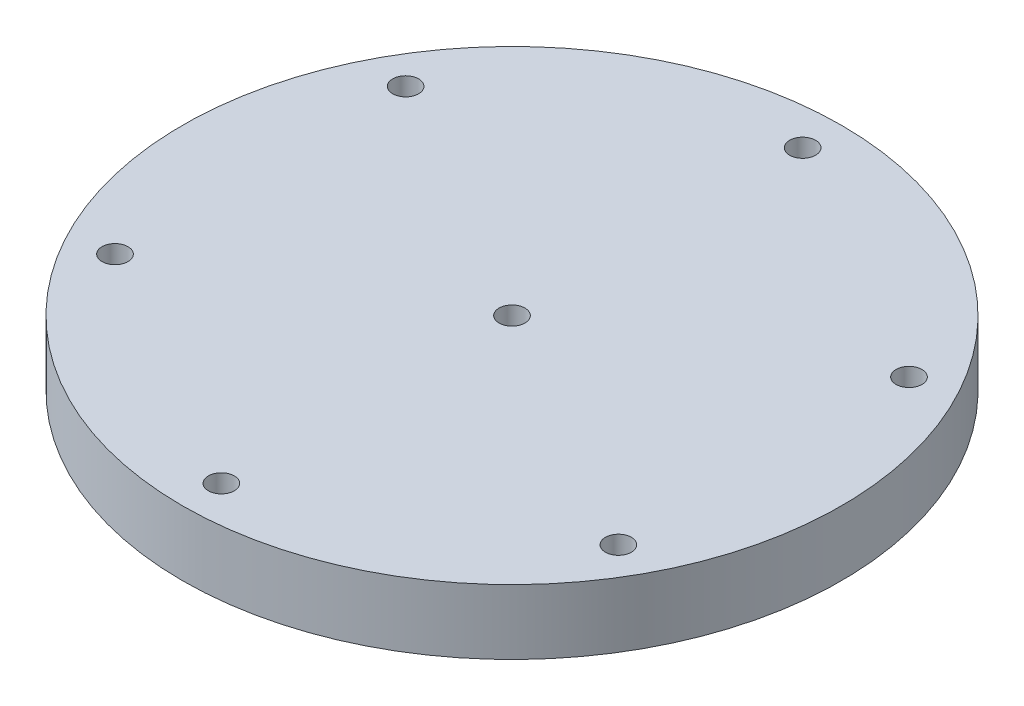
SolidWorks part; units mm, degrees
ref_plane "Front Plane" through (0, 0, 0) normal (0, 0, 1) x (1, 0, 0)
ref_plane "Top Plane" through (0, 0, 0) normal (0, 1, 0) x (1, 0, 0)
ref_plane "Right Plane" through (0, 0, 0) normal (1, 0, 0) x (0, 0, -1)
sketch "Sketch1" plane through (0, 0, 0) normal (0, 1, 0) x (1, 0, 0)
  circle A0 centre (0, 0) radius 50.8
  dimension "D1" = 101.6
extrude "Boss-Extrude1" add sketch "Sketch1" along normal blind 10
sketch "Sketch2" plane through (0, 0, 0) normal (0, -1, 0) x (1, 0, 0)
  circle A0 centre (0, 0) radius 38.1
  circle A1 centre (0, 0) radius 36.5
  dimension "D1" = 76.2
  dimension "D2" = 1.6
extrude "Cut-Extrude1" cut sketch "Sketch2" against normal blind 2
sketch "Sketch3" plane through (0, 10, 0) normal (0, 1, 0) x (1, 0, 0)
  line L0 (0, 0) -> (0, 50.8) construction
  circle A0 centre (0, 0) radius 2
  circle A1 centre (0, 0) radius 50.8 construction
  circle A2 centre (0, 44.8) radius 2
  circle A3 centre (38.7979, 22.4) radius 2
  circle A4 centre (38.7979, -22.4) radius 2
  circle A5 centre (0, -44.8) radius 2
  circle A6 centre (-38.7979, -22.4) radius 2
  circle A7 centre (-38.7979, 22.4) radius 2
  point P22 (0, 0)
  dimension "D1" = 4
  dimension "D2" = 4
  dimension "D3" = 6
  dimension "D4" = 6
extrude "Cut-Extrude2" cut sketch "Sketch3" against normal blind 14
